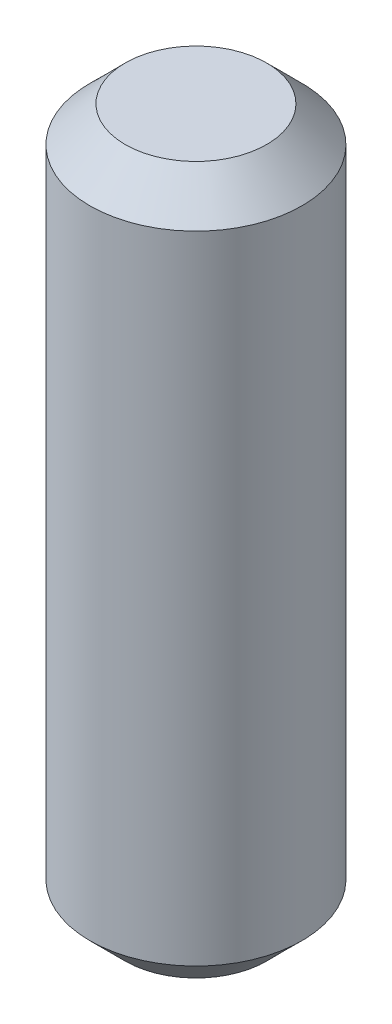
SolidWorks part; units mm, degrees
ref_plane "Front Plane" through (0, 0, 0) normal (0, 0, 1) x (1, 0, 0)
ref_plane "Top Plane" through (0, 0, 0) normal (0, 1, 0) x (1, 0, 0)
ref_plane "Right Plane" through (0, 0, 0) normal (1, 0, 0) x (0, 0, -1)
sketch "Sketch1" plane through (0, 0, 0) normal (0, 1, 0) x (1, 0, 0)
  circle A0 centre (0, 0) radius 1.5
  dimension "D1" = 3
extrude "Boss-Extrude1" add sketch "Sketch1" along normal blind 10
chamfer "Chamfer1" distance 0.5 angle 45 2 edges at (0, 0, 1.5) (0, 10, 1.5)
